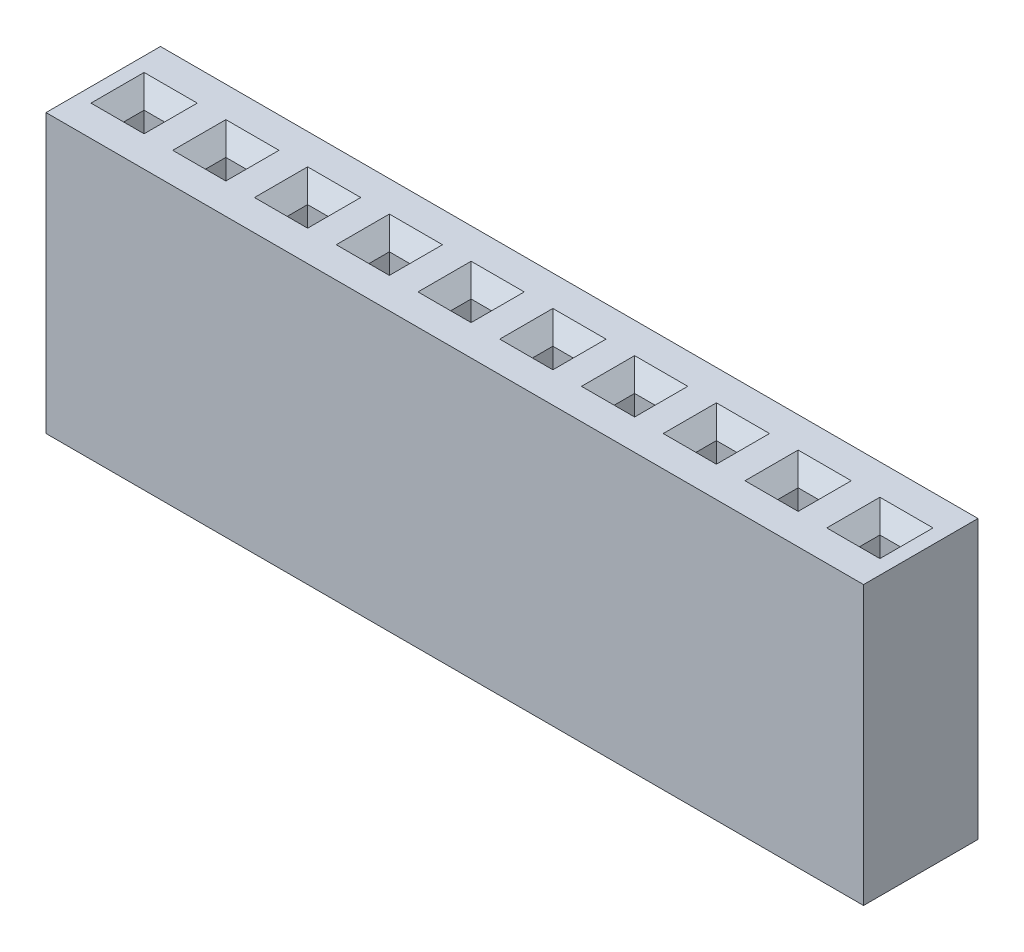
SolidWorks part; units mm, degrees
material "ABS PC"
ref_plane "Front Plane" through (0, 0, 0) normal (0, 0, 1) x (1, 0, 0)
ref_plane "Top Plane" through (0, 0, 0) normal (0, 1, 0) x (1, 0, 0)
ref_plane "Right Plane" through (0, 0, 0) normal (1, 0, 0) x (0, 0, -1)
sketch "Sketch1" plane through (0, 0, 0) normal (0, 1, 0) x (1, 0, 0)
  line L1 (0, 0) -> (25.4, 0)
  line L2 (0, 0) -> (0, 3.556)
  line L3 (0, 3.556) -> (25.4, 3.556)
  line L4 (25.4, 0) -> (25.4, 3.556)
  dimension "D1" = 3.556
  dimension "D2" = 25.4
extrude "Boss-Extrude1" add sketch "Sketch1" along normal blind 8.636
sketch "Sketch2" plane through (0, 8.636, 0) normal (0, 1, 0) x (1, 0, 0)
  line L0 (0, 0) -> (25.4, 0) construction
  line L1 (0.9525, 2.0955) -> (1.5875, 2.0955)
  line L2 (0.9525, 2.0955) -> (0.9525, 1.4605)
  line L3 (0.9525, 1.4605) -> (1.5875, 1.4605)
  line L4 (1.5875, 2.0955) -> (1.5875, 1.4605)
  line L5 (0.9525, 2.0955) -> (1.5875, 1.4605) construction
  line L6 (0.9525, 1.4605) -> (1.5875, 2.0955) construction
  line L7 (0, 3.556) -> (0, 0) construction
  point P0 (1.27, 1.778)
  dimension "D1" = 0.635
  dimension "D2" = 0.635
  dimension "D3" = 1.778
  dimension "D4" = 1.27
extrude "Cut-Extrude1" cut sketch "Sketch2" against normal blind 6.35
chamfer "Chamfer1" distance 0.508 angle 45 4 edges at (0.9525, 8.636, -1.778) (1.27, 8.636, -1.4605) (1.5875, 8.636, -1.778) (1.27, 8.636, -2.0955)
pattern_linear "LPattern1" count 10 spacing 2.54 along (1, 0, 0) of "Cut-Extrude1", "Chamfer1"
